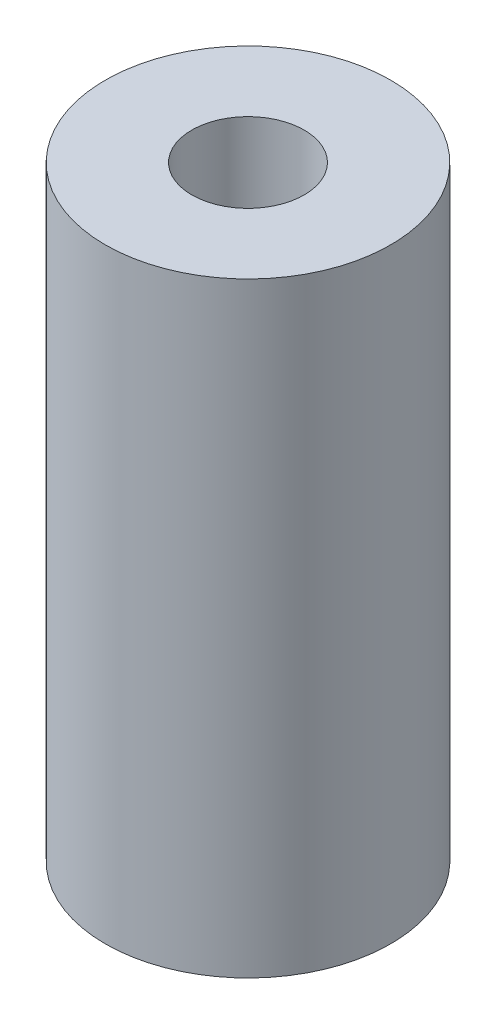
SolidWorks part; units mm, degrees
ref_plane "Front Plane" through (0, 0, 0) normal (0, 0, 1) x (1, 0, 0)
ref_plane "Top Plane" through (0, 0, 0) normal (0, 1, 0) x (1, 0, 0)
ref_plane "Right Plane" through (0, 0, 0) normal (1, 0, 0) x (0, 0, -1)
sketch "Sketch1" plane through (0, 0, 0) normal (0, 1, 0) x (1, 0, 0)
  circle A0 centre (0, 0) radius 1.651
  circle A1 centre (0, 0) radius 4.191
  point P5 (0, 0)
  point P6 (0, 0)
  dimension "D1" = 2.54
  dimension "D2" = 3.302
extrude "Boss-Extrude1" add sketch "Sketch1" along normal blind 17.78 contours A0 | A1
